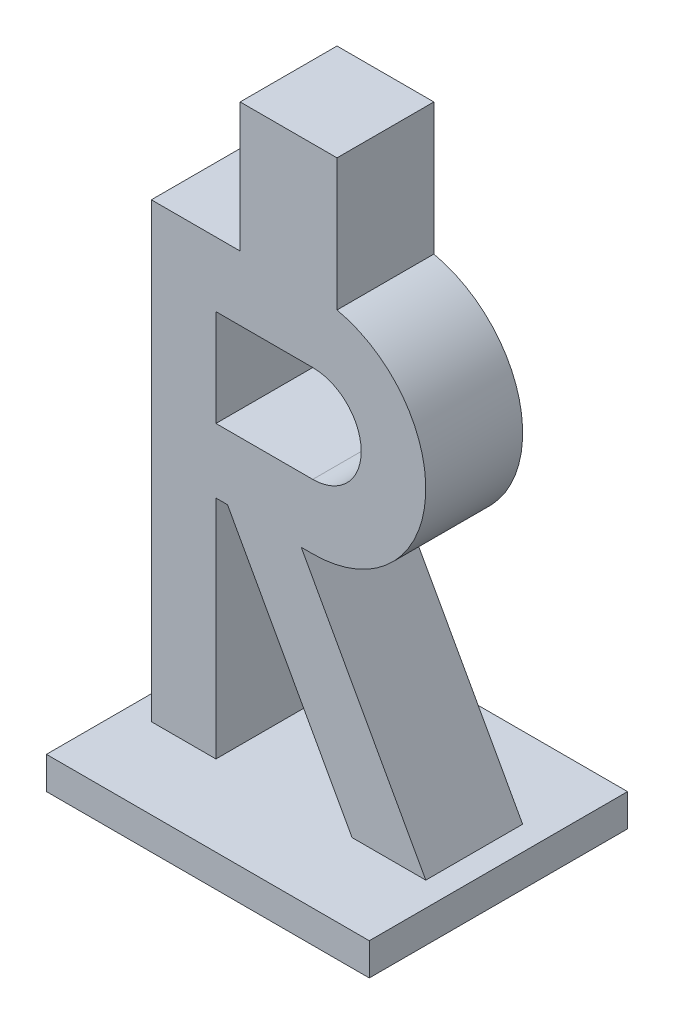
SolidWorks part; units mm, degrees
ref_plane "Vorne" through (0, 0, 0) normal (0, 0, 1) x (1, 0, 0)
ref_plane "Oben" through (0, 0, 0) normal (0, 1, 0) x (1, 0, 0)
ref_plane "Rechts" through (0, 0, 0) normal (1, 0, 0) x (0, 0, -1)
sketch "Skizze1" plane through (0, 0, 0) normal (0, 0, 1) x (1, 0, 0)
  line L0 (0, 0) -> (0, 70)
  line L1 (0, 70) -> (25, 70)
  line L6 (10, 35) -> (10, 0)
  line L7 (10, 0) -> (0, 0)
  line L8 (10, 60) -> (10, 45)
  line L9 (10, 45) -> (25, 45)
  line L10 (25, 60) -> (10, 60)
  line L11 (25, 35) -> (23.2092, 35)
  line L12 (23.2092, 35) -> (42.5, 0)
  line L13 (42.5, 0) -> (31.0817, 0)
  line L14 (31.0817, 0) -> (11.7908, 35)
  line L15 (11.7908, 35) -> (10, 35)
  arc A0 (25, 70) -> (25, 35) centre (25, 52.5) cw
  arc A1 (25, 45) -> (25, 60) centre (25, 52.5) ccw
  point P18 (42.5, 52.5)
  dimension "D4" = 17.5
  dimension "D6" = 7.5
  dimension "D1" = 70
  dimension "D2" = 10
  dimension "D3" = 25
  dimension "D5" = 10
extrude "Aufsatz-Linear austragen1" add sketch "Skizze1" along normal blind 15
sketch "Skizze2" plane through (0, 0, 0) normal (0, -1, 0) x (1, 0, 0)
  line L0 (-7.7774, 7.5) -> (46.4698, 7.5) construction
  line L1 (21.25, 20.1207) -> (21.25, -2.7666) construction
  line L2 (0, 0) -> (10, 0) construction
  line L3 (-3.75, 27.5) -> (46.25, 27.5)
  line L4 (-3.75, 27.5) -> (-3.75, -12.5)
  line L5 (-3.75, -12.5) -> (46.25, -12.5)
  line L6 (46.25, 27.5) -> (46.25, -12.5)
  line L7 (0, 15) -> (10, 15) construction
  line L8 (0, 15) -> (0, 0) construction
  line L9 (42.5, 15) -> (42.5, 0) construction
  dimension "D1" = 40
  dimension "D2" = 50
extrude "Aufsatz-Linear austragen2" add sketch "Skizze2" along normal blind 5
sketch "Skizze6" plane through (0, 0, 15) normal (0, 0, 1) x (1, 0, 0)
  line L0 (-12.3157, 35) -> (58.1379, 35) construction
  line L1 (21.25, -7.1747) -> (21.25, 75.4222) construction
  line L2 (0, 0) -> (10, 0) construction
  line L3 (25, 70) -> (0, 70) construction
  line L4 (-3.75, -5) -> (-3.75, 0) construction
  line L5 (28.75, 69.5935) -> (13.75, 69.5935)
  line L6 (28.75, 69.5935) -> (28.75, 90)
  line L7 (28.75, 90) -> (13.75, 90)
  line L8 (13.75, 69.5935) -> (13.75, 90)
  line L9 (46.25, -5) -> (46.25, 0) construction
  arc A0 (25, 35) -> (25, 70) centre (25, 52.5) ccw construction
  point P17 (13.75, 70)
  dimension "D1" = 15
  dimension "D2" = 20
extrude "Aufsatz-Linear austragen3" add sketch "Skizze6" against normal blind 15
